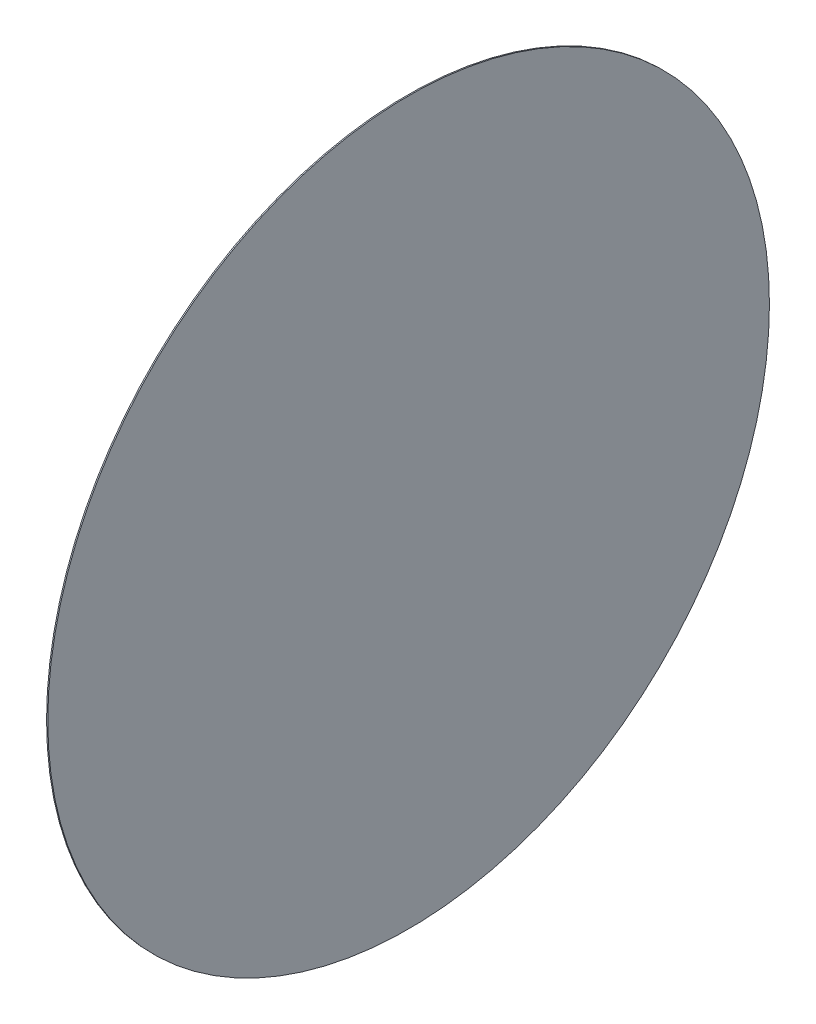
SolidWorks part; units mm, degrees
ref_plane "前视基准面" through (0, 0, 0) normal (0, 0, 1) x (1, 0, 0)
ref_plane "上视基准面" through (0, 0, 0) normal (0, 1, 0) x (1, 0, 0)
ref_plane "右视基准面" through (0, 0, 0) normal (1, 0, 0) x (0, 0, -1)
sketch "草图1" plane through (0, 0, 0) normal (0, 0, 1) x (1, 0, 0)
  line L0 (0, 9) -> (0, 0)
  line L2 (0, 9) -> (0.03, 9)
  line L3 (0, 0) -> (0.03, 0)
  line L4 (0.03, 9) -> (0.03, 0)
  dimension "D1" = 9
  dimension "D2" = 0.03
revolve "旋转2" add sketch "草图1" angle 360 about L3
